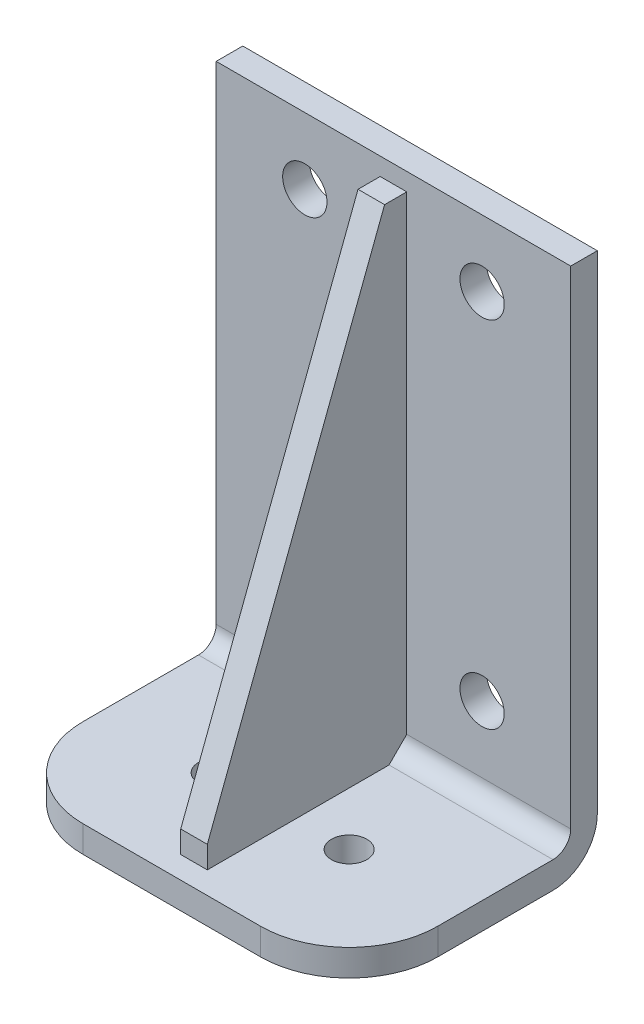
SolidWorks part; units mm, degrees
material "普通碳钢"
ref_plane "前视基准面" through (0, 0, 0) normal (0, 0, 1) x (1, 0, 0)
ref_plane "上视基准面" through (0, 0, 0) normal (0, 1, 0) x (1, 0, 0)
ref_plane "右视基准面" through (0, 0, 0) normal (1, 0, 0) x (0, 0, -1)
sketch "草图1" plane through (0, 0, 0) normal (0, 0, 1) x (1, 0, 0)
  line L2 (0, 0) -> (80, 0)
  line L3 (0, 0) -> (0, 120)
  line L4 (0, 120) -> (80, 120)
  line L5 (80, 0) -> (80, 120)
  dimension "D1" = 80
  dimension "D2" = 120
extrude "凸台-拉伸1" add sketch "草图1" along normal blind 6
sketch "草图2" plane through (0, 0, 6) normal (0, 0, 1) x (1, 0, 0)
  line L0 (0, 120) -> (0, 0) construction
  line L1 (0, 0) -> (80, 0)
  line L2 (0, 0) -> (0, 6)
  line L3 (0, 6) -> (80, 6)
  line L4 (80, 0) -> (80, 6)
  line L5 (80, 0) -> (80, 120) construction
  line L6 (0, 0) -> (80, 0) construction
  dimension "D1" = 6
extrude "凸台-拉伸2" add sketch "草图2" along normal blind 50
fillet "圆角1" radius 4 1 edges at (40, 6, 6)
fillet "圆角2" radius 10 1 edges at (40, 0, 0)
sketch "草图3" plane through (0, 0, 6) normal (0, 0, 1) x (1, 0, 0)
  line L0 (40, 120) -> (40, -2.2798) construction
  line L1 (80, 120) -> (0, 120) construction
  line L2 (20, 105) -> (60, 105) construction
  line L3 (20, 105) -> (20, 25) construction
  line L4 (20, 25) -> (60, 25) construction
  line L5 (60, 105) -> (60, 25) construction
  circle A0 centre (60, 105) radius 5
  circle A1 centre (20, 105) radius 5
  circle A2 centre (20, 25) radius 5
  circle A3 centre (60, 25) radius 5
  dimension "D4" = 10
  dimension "D1" = 40
  dimension "D2" = 80
  dimension "D3" = 15
extrude "切除-拉伸1" cut sketch "草图3" against normal up to next
ref_plane "基准面4" through (40, 0, 0) normal (1, 0, 0) x (0, 0, -1)
sketch "草图4" plane through (40, 0, 0) normal (1, 0, 0) x (0, 0, -1)
  line L0 (-51, 6) -> (-10, 6)
  line L1 (-10, 6) -> (-6, 10)
  line L2 (-6, 10) -> (-6, 116)
  line L3 (-6, 116) -> (-11, 116)
  line L4 (-11, 116) -> (-51, 11)
  line L5 (-51, 11) -> (-51, 6)
  point P3 (-8.5, 116)
  dimension "D1" = 45
  dimension "D2" = 4
  dimension "D3" = 4
  dimension "D4" = 110
  dimension "D5" = 5
  dimension "D6" = 5
extrude "凸台-拉伸3" add sketch "草图4" along normal mid plane 6
sketch "草图5" plane through (0, 6, 0) normal (0, 1, 0) x (1, 0, 0)
  line L0 (55, -31) -> (25, -31) construction
  line L1 (0, -56) -> (0, -10) construction
  line L2 (80, -56) -> (80, -10) construction
  line L3 (80, -56) -> (0, -56) construction
  circle A0 centre (25, -31) radius 4
  circle A1 centre (55, -31) radius 4
  dimension "D1" = 8
  dimension "D2" = 8
  dimension "D3" = 25
  dimension "D4" = 25
  dimension "D5" = 25
extrude "切除-拉伸2" cut sketch "草图5" against normal blind 6
fillet "圆角3" radius 20 2 edges at (0, 3, 56) (80, 3, 56)
